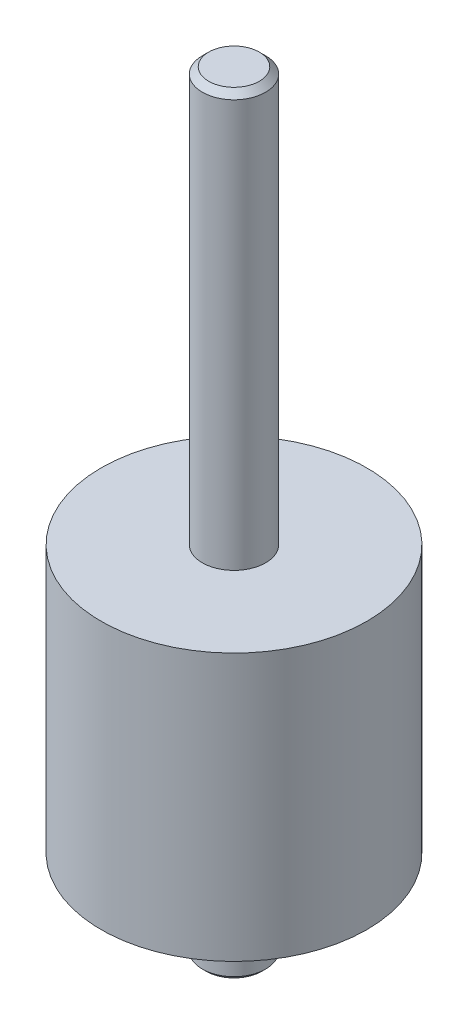
SolidWorks part; units mm, degrees
ref_plane "Front Plane" through (0, 0, 0) normal (0, 0, 1) x (1, 0, 0)
ref_plane "Top Plane" through (0, 0, 0) normal (0, 1, 0) x (1, 0, 0)
ref_plane "Right Plane" through (0, 0, 0) normal (1, 0, 0) x (0, 0, -1)
sketch "Sketch1" plane through (0, 0, 0) normal (0, 0, 1) x (1, 0, 0)
  line L0 (0, -38.6) -> (2.5, -38.6)
  line L1 (2.5, -38.6) -> (2.5, -31.6)
  line L2 (2.5, -31.6) -> (10.5, -31.6)
  line L3 (10.5, -31.6) -> (10.5, -10.5)
  line L4 (10.5, -10.5) -> (2.5, -10.5)
  line L5 (2.5, -10.5) -> (2.5, 22.2)
  line L6 (2.5, 22.2) -> (0, 22.2)
  line L7 (0, 22.2) -> (0, -38.6)
  dimension "D1" = 38.6
  dimension "D2" = 2.5
  dimension "D3" = 7
  dimension "D4" = 10.5
  dimension "D5" = 21.1
  dimension "D6" = 22.2
revolve "Revolve1" add sketch "Sketch1" angle 360 about L7
chamfer "Chamfer1" distance 0.3 angle 45 1 edges at (-2.5, -38.6, 0)
chamfer "Chamfer2" distance 0.5 angle 45 1 edges at (-2.5, 22.2, 0)
